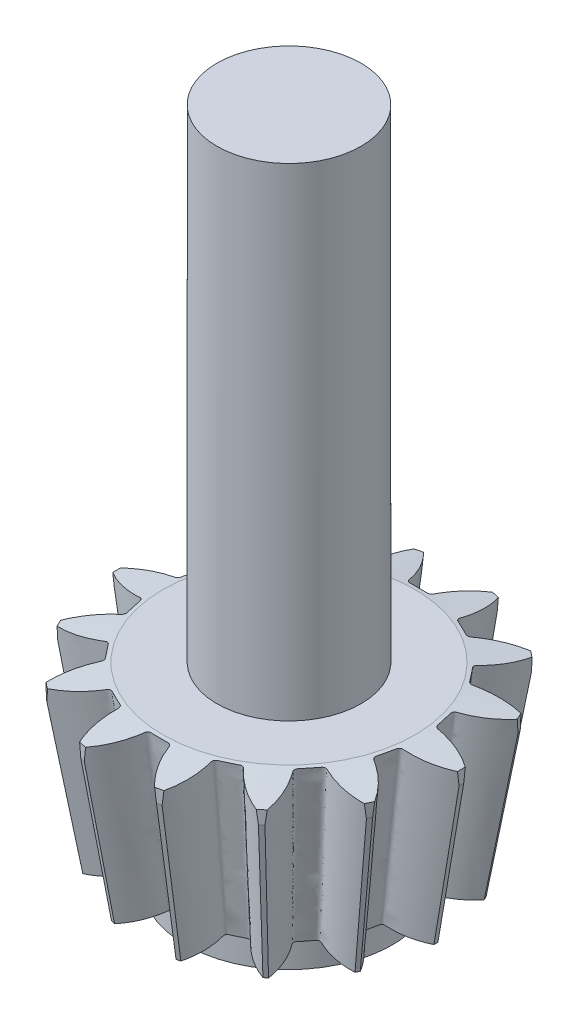
SolidWorks part; units mm, degrees
ref_plane "Front Plane" through (0, 0, 0) normal (0, 0, 1) x (1, 0, 0)
ref_plane "Top Plane" through (0, 0, 0) normal (0, 1, 0) x (1, 0, 0)
ref_plane "Right Plane" through (0, 0, 0) normal (1, 0, 0) x (0, 0, -1)
sketch "Sketch1" plane through (0, 0, 0) normal (0, 0, 1) x (1, 0, 0)
  line L0 (0, 0) -> (0, -75.1876) construction
  line L1 (0, 0) -> (9.1333, 0)
  line L2 (0, 0) -> (0, -11.9144)
  line L3 (0, -11.9144) -> (7.686, -11.9144)
  line L4 (0, -75.1876) -> (10.5, -0.1913) construction
  line L5 (9.1333, 0) -> (12.6589, -0.4936)
  line L6 (0, -75.1876) -> (12.6589, -0.4936) construction
  line L7 (0, -75.1876) -> (9.1333, 0) construction
  line L8 (12.6589, -0.4936) -> (10.653, -12.3298)
  line L9 (10.653, -12.3298) -> (7.686, -11.9144)
  line L11 (10.5, -0.1913) -> (0, -0.1913) construction
  dimension "D1" = 2.18
  dimension "D2" = 10.5
  dimension "D3" = 1.38
  dimension "D4" = 12
  dimension "D5" = 7.97
  dimension "D6" = 7.686
  dimension "D7" = 75.1876
  dimension "D8" = 75.7278
  dimension "D9" = 1.649
revolve "Revolve1" add sketch "Sketch1" angle 360 about L0
ref_plane "Plane1" through (0, 1.2541, 0.1756) normal (0, 0.9903, 0.1387) x (1, 0, 0)
ref_plane "Plane2" through (0, -73.785, -10.3304) normal (0, 0.9903, 0.1387) x (1, 0, 0)
sketch "Sketch2" plane through (0, 1.2541, 0.1756) normal (0, 0.9903, 0.1387) x (1, 0, 0)
  line L0 (0, 4.5573) -> (133.355, -837.4128) construction
  line L1 (0, 4.5573) -> (75.4188, -932.497) construction
  line L2 (0, -170.139) -> (0, 4.5573) construction
  line L3 (-67.5504, -12.6051) -> (67.5504, -12.6051) construction
  line L4 (2.3465, -10.258) -> (1.1998, -10.3503) construction
  arc A0 (-3.0757, -12.676) -> (3.0757, -12.676) centre (0, 4.5573) ccw
  arc A1 (-0.6074, -9.3088) -> (0.6074, -9.3088) centre (0, 4.5573) ccw
  circle A2 centre (0, 4.5573) radius 15 construction
  circle A3 centre (0, 4.5573) radius 14.0954 construction
  arc A4 (0.8919, -9.5138) -> (0.6074, -9.3088) centre (0.6198, -9.5915) ccw
  arc A5 (0.8919, -9.5138) -> (3.0757, -12.676) centre (6.6609, -7.865) ccw
  arc A6 (-3.0757, -12.676) -> (-0.8919, -9.5138) centre (-6.6609, -7.865) ccw
  arc A7 (-0.6074, -9.3088) -> (-0.8919, -9.5138) centre (-0.6198, -9.5915) ccw
  ellipse E7 centre (0, -0.0684) end of major axis (12.6589, -0.0684) minor radius 12.5367 construction
  point P21 (0, -12.6051)
  dimension "D2" = 35.0113
  dimension "D3" = 27.7588
  dimension "D4" = 30
  dimension "D5" = 28.1908
  dimension "D8" = 6
  dimension "D9" = 0.283
  dimension "D1" = 17.1624
  dimension "D6" = 9
  dimension "D7" = 1.1504
sketch "Sketch3" plane through (0, -73.785, -10.3304) normal (0, 0.9903, 0.1387) x (1, 0, 0)
  line L0 (0, -12.6051) -> (0, 0) construction
  line L1 (21.082, -9.0451) -> (-20.32, -9.0451) construction
  line L2 (0, -170.139) -> (0, 4.5573) construction
  circle A0 centre (0, -10.4281) radius 0.0127
  ellipse E0 centre (0, 0) end of major axis (9.1333, 0) minor radius 9.0451 construction
  ellipse E1 centre (0, -0.0684) end of major axis (12.6589, -0.0684) minor radius 12.5367 construction
  dimension "D2" = 0.0254
  dimension "D1" = 1.383
loft "Cut-Loft1" cut profiles "Sketch3", "Sketch2"
pattern_circular "CirPattern2" count 14 every 25.714 about axis through (0, 0, 0) along (0, -1, 0) of "Cut-Loft1"
sketch "Sketch5" plane through (0, 0, 0) normal (0, 0, 1) x (1, 0, 0)
  line L0 (0, 13.8442) -> (0, -28)
  line L1 (0, 25.41) -> (0, 23.5) construction
  line L3 (4.6, 16.5) -> (0, 13.8442)
  line L4 (4.6, 16.5) -> (0, 16.5) construction
  line L5 (0, 13.8442) -> (0, 16.5) construction
  line L6 (0, 16.5) -> (0, 23.5) construction
  line L7 (4.6, 16.5) -> (4.6, 23.872)
  line L8 (9.5, 16.5) -> (4.6, 16.5) construction
  line L14 (0, 0) -> (0, 25.41) construction
  line L15 (7.5, 24.5) -> (8.5, 24.5)
  line L16 (8.5, 24.5) -> (12.5, 23.4282)
  line L17 (12.5, 23.4282) -> (12.5, 16.5)
  line L18 (12.5, 16.5) -> (9.5, 16.5)
  line L19 (7.5, 14.5) -> (7.5, 13.5)
  line L20 (9.5, 11.5) -> (12.5, 11.5)
  line L21 (12.5, 11.5) -> (12.5, 4.5)
  line L22 (12.5, 4.5) -> (9.5, 4.5)
  line L23 (7.5, 2.5) -> (7.5, 0)
  line L24 (0, 0) -> (9.1333, 0) construction
  line L25 (12.6589, -0.4936) -> (0, -0.4936) construction
  line L26 (0, 0) -> (0, -11.9144) construction
  line L27 (0, 0) -> (0, -28) construction
  line L28 (0, 0) -> (0, -75.1876) construction
  line L29 (0, -28) -> (5, -28)
  line L31 (5, -28) -> (5, -16)
  line L32 (7, -14) -> (7.5, -14)
  line L33 (7.5, -14) -> (7.5, 0)
  arc A0 (7.5, 24.5) -> (4.6, 23.872) centre (0, 52.125) cw
  arc A1 (4.6, 23.872) -> (0, 23.5) centre (0, 52.125) cw construction
  arc A4 (9.5, 16.5) -> (7.5, 14.5) centre (9.5, 14.5) ccw
  arc A5 (7.5, 13.5) -> (9.5, 11.5) centre (9.5, 13.5) ccw
  arc A6 (9.5, 4.5) -> (7.5, 2.5) centre (9.5, 2.5) ccw
  arc A7 (5, -16) -> (7, -14) centre (7, -16) cw
  point P0 (4.5667, 0)
  point P36 (12.5, 19.9641)
  point P58 (7.5, 16.5)
  point P61 (7.5, 11.5)
  dimension "D21" = 2
  dimension "D22" = 9.2
  dimension "D3" = 20
  dimension "D4" = 4.5
  dimension "D5" = 28
  dimension "D6" = 7.5
  dimension "D7" = 24.5
  dimension "D8" = 25
  dimension "D9" = 15
  dimension "D10" = 8
  dimension "D11" = 7
  dimension "D12" = 15
  dimension "D13" = 5
  dimension "D14" = 4
  dimension "D15" = 25.3179
  dimension "D16" = 1
  dimension "D17" = 60
  dimension "D18" = 10
  dimension "D20" = 14
revolve "Revolve2" add sketch "Sketch5" angle 360 about L0
sketch "Sketch6" plane through (0, 24.5, 0) normal (0, 1, 0) x (1, 0, 0)
  line L1 (-4.6, -4.6) -> (4.6, -4.6)
  line L2 (-4.6, -4.6) -> (-4.6, 4.6)
  line L3 (-4.6, 4.6) -> (4.6, 4.6)
  line L4 (4.6, -4.6) -> (4.6, 4.6)
  line L5 (-4.6, -4.6) -> (4.6, 4.6) construction
  line L6 (-4.6, 4.6) -> (4.6, -4.6) construction
  circle A0 centre (0, 0) radius 4.6 construction
  point P0 (0, 0)
sketch "Sketch7" plane through (0, 0, 0) normal (0, 1, 0) x (1, 0, 0)
  circle A0 centre (0, 0) radius 12.5 construction
  circle A1 centre (0, 0) radius 12.5
extrude "Cut-Extrude2" cut sketch "Sketch7" against normal blind 3 flip side to cut
sketch "Sketch8" plane through (0, 0, 0) normal (0, 1, 0) x (1, 0, 0)
  line L1 (-33.5203, -41.9848) -> (24.4416, -41.9848)
  line L2 (-33.5203, -41.9848) -> (-33.5203, 44.1028)
  line L3 (-33.5203, 44.1028) -> (24.4416, 44.1028)
  line L4 (24.4416, -41.9848) -> (24.4416, 44.1028)
extrude "Cut-Extrude3" cut sketch "Sketch8" along normal through all
sketch "Sketch9" plane through (0, -28, 0) normal (0, -1, 0) x (1, 0, 0)
  line L1 (12.1979, 21.6415) -> (-10.7063, 21.6415)
  line L2 (12.1979, 21.6415) -> (12.1979, -17.7509)
  line L3 (12.1979, -17.7509) -> (-10.7063, -17.7509)
  line L4 (-10.7063, 21.6415) -> (-10.7063, -17.7509)
extrude "Cut-Extrude4" cut sketch "Sketch9" against normal up to surface (14 mm away)
sketch "Sketch10" plane through (0, 0, 0) normal (0, 1, 0) x (1, 0, 0)
  circle A0 centre (0, 0) radius 5.2225
extrude "Boss-Extrude1" add sketch "Sketch10" along normal blind 35
